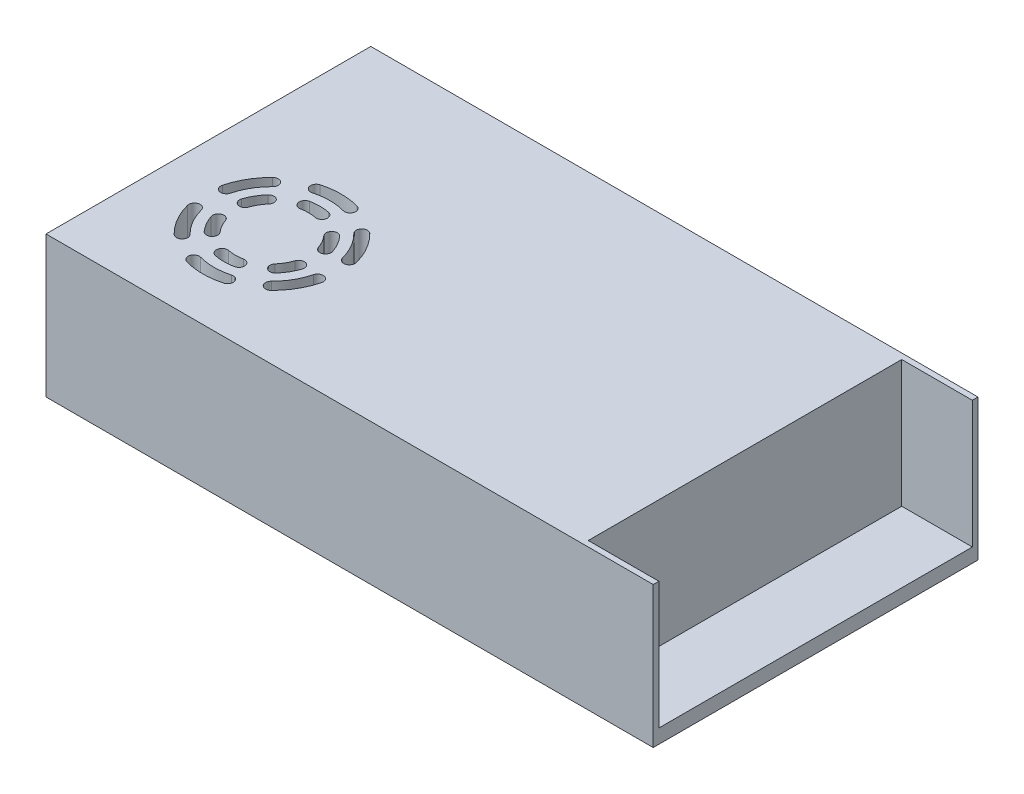
SolidWorks part; units mm, degrees
material "Простая углеродистая сталь"
ref_plane "Спереди" through (0, 0, 0) normal (0, 0, 1) x (1, 0, 0)
ref_plane "Сверху" through (0, 0, 0) normal (0, 1, 0) x (1, 0, 0)
ref_plane "Справа" through (0, 0, 0) normal (1, 0, 0) x (0, 0, -1)
sketch "Эскиз1" plane through (0, 0, 0) normal (0, 1, 0) x (1, 0, 0)
  line L0 (0, 0) -> (215, 0)
  line L1 (0, 0) -> (0, 115)
  line L2 (215, 0) -> (215, 115)
  line L3 (0, 115) -> (215, 115)
  dimension "D1" = 115
  dimension "D2" = 215
extrude "Бобышка-Вытянуть1" add sketch "Эскиз1" along normal blind 50
sketch "Эскиз2" plane through (0, 50, 0) normal (0, 1, 0) x (1, 0, 0)
  line L0 (215, 2) -> (190, 2)
  line L1 (215, 2) -> (215, 113)
  line L2 (190, 2) -> (190, 113)
  line L3 (215, 113) -> (190, 113)
  line L4 (215, 0) -> (215, 115) construction
  line L5 (215, 115) -> (0, 115) construction
  line L6 (0, 0) -> (215, 0) construction
  dimension "D1" = 2
  dimension "D2" = 2
  dimension "D3" = 25
extrude "Вырез-Вытянуть1" cut sketch "Эскиз2" against normal blind 45
sketch "Эскиз3" plane through (0, 50, 0) normal (0, 1, 0) x (1, 0, 0)
  line L0 (0, 115) -> (0, 0) construction
  line L1 (0, 0) -> (215, 0) construction
  line L2 (40, 17.5) -> (40, 62.5) construction
  circle A0 centre (40, 40) radius 22.5 construction
  arc A1 (37, 25.3031) -> (43, 25.3031) centre (40, 40) ccw construction
  arc A2 (36.6, 23.3435) -> (43.4, 23.3435) centre (40, 40) ccw
  circle A3 centre (40, 40) radius 15 construction
  arc A4 (37.4, 27.2627) -> (42.6, 27.2627) centre (40, 40) ccw
  arc A5 (37.4, 27.2627) -> (36.6, 23.3435) centre (37, 25.3031) ccw
  arc A6 (43.4, 23.3435) -> (42.6, 27.2627) centre (43, 25.3031) ccw
  arc A7 (25.7721, 35.2496) -> (28.7721, 30.0535) centre (40, 40) ccw construction
  arc A8 (23.875, 34.6162) -> (27.275, 28.7272) centre (40, 40) ccw
  arc A9 (27.6691, 35.883) -> (30.2691, 31.3797) centre (40, 40) ccw
  arc A10 (27.6691, 35.883) -> (23.875, 34.6162) centre (25.7721, 35.2496) ccw
  arc A11 (27.275, 28.7272) -> (30.2691, 31.3797) centre (28.7721, 30.0535) ccw
  arc A14 (28.7721, 49.9465) -> (25.7721, 44.7504) centre (40, 40) ccw construction
  arc A15 (27.275, 51.2728) -> (23.875, 45.3838) centre (40, 40) ccw
  arc A16 (30.2691, 48.6203) -> (27.6691, 44.117) centre (40, 40) ccw
  arc A17 (30.2691, 48.6203) -> (27.275, 51.2728) centre (28.7721, 49.9465) ccw
  arc A18 (23.875, 45.3838) -> (27.6691, 44.117) centre (25.7721, 44.7504) ccw
  arc A19 (43, 54.6969) -> (37, 54.6969) centre (40, 40) ccw construction
  arc A20 (43.4, 56.6565) -> (36.6, 56.6565) centre (40, 40) ccw
  arc A21 (42.6, 52.7373) -> (37.4, 52.7373) centre (40, 40) ccw
  arc A22 (42.6, 52.7373) -> (43.4, 56.6565) centre (43, 54.6969) ccw
  arc A23 (36.6, 56.6565) -> (37.4, 52.7373) centre (37, 54.6969) ccw
  arc A24 (54.2279, 44.7504) -> (51.2279, 49.9465) centre (40, 40) ccw construction
  arc A25 (56.125, 45.3838) -> (52.725, 51.2728) centre (40, 40) ccw
  arc A26 (52.3309, 44.117) -> (49.7309, 48.6203) centre (40, 40) ccw
  arc A27 (52.3309, 44.117) -> (56.125, 45.3838) centre (54.2279, 44.7504) ccw
  arc A28 (52.725, 51.2728) -> (49.7309, 48.6203) centre (51.2279, 49.9465) ccw
  arc A29 (51.2279, 30.0535) -> (54.2279, 35.2496) centre (40, 40) ccw construction
  arc A30 (52.725, 28.7272) -> (56.125, 34.6162) centre (40, 40) ccw
  arc A31 (49.7309, 31.3797) -> (52.3309, 35.883) centre (40, 40) ccw
  arc A32 (49.7309, 31.3797) -> (52.725, 28.7272) centre (51.2279, 30.0535) ccw
  arc A33 (56.125, 34.6162) -> (52.3309, 35.883) centre (54.2279, 35.2496) ccw
  arc A34 (34, 18.3148) -> (46, 18.3148) centre (40, 40) ccw construction
  arc A35 (33.4667, 16.3872) -> (46.5333, 16.3872) centre (40, 40) ccw
  arc A36 (34.5333, 20.2423) -> (45.4667, 20.2423) centre (40, 40) ccw
  arc A37 (34.5333, 20.2423) -> (33.4667, 16.3872) centre (34, 18.3148) ccw
  arc A38 (46.5333, 16.3872) -> (45.4667, 20.2423) centre (46, 18.3148) ccw
  arc A39 (18.22, 34.3535) -> (24.22, 23.9612) centre (40, 40) ccw construction
  arc A40 (16.284, 33.8516) -> (22.8174, 22.5356) centre (40, 40) ccw
  arc A41 (20.156, 34.8554) -> (25.6227, 25.3869) centre (40, 40) ccw
  arc A42 (20.156, 34.8554) -> (16.284, 33.8516) centre (18.22, 34.3535) ccw
  arc A43 (22.8174, 22.5356) -> (25.6227, 25.3869) centre (24.22, 23.9612) ccw
  arc A44 (24.22, 56.0388) -> (18.22, 45.6465) centre (40, 40) ccw construction
  arc A45 (22.8174, 57.4644) -> (16.284, 46.1484) centre (40, 40) ccw
  arc A46 (25.6227, 54.6131) -> (20.156, 45.1446) centre (40, 40) ccw
  arc A47 (25.6227, 54.6131) -> (22.8174, 57.4644) centre (24.22, 56.0388) ccw
  arc A48 (16.284, 46.1484) -> (20.156, 45.1446) centre (18.22, 45.6465) ccw
  arc A49 (46, 61.6852) -> (34, 61.6852) centre (40, 40) ccw construction
  arc A50 (46.5333, 63.6128) -> (33.4667, 63.6128) centre (40, 40) ccw
  arc A51 (45.4667, 59.7577) -> (34.5333, 59.7577) centre (40, 40) ccw
  arc A52 (45.4667, 59.7577) -> (46.5333, 63.6128) centre (46, 61.6852) ccw
  arc A53 (33.4667, 63.6128) -> (34.5333, 59.7577) centre (34, 61.6852) ccw
  arc A54 (61.78, 45.6465) -> (55.78, 56.0388) centre (40, 40) ccw construction
  arc A55 (63.716, 46.1484) -> (57.1826, 57.4644) centre (40, 40) ccw
  arc A56 (59.844, 45.1446) -> (54.3773, 54.6131) centre (40, 40) ccw
  arc A57 (59.844, 45.1446) -> (63.716, 46.1484) centre (61.78, 45.6465) ccw
  arc A58 (57.1826, 57.4644) -> (54.3773, 54.6131) centre (55.78, 56.0388) ccw
  arc A59 (55.78, 23.9612) -> (61.78, 34.3535) centre (40, 40) ccw construction
  arc A60 (57.1826, 22.5356) -> (63.716, 33.8516) centre (40, 40) ccw
  arc A61 (54.3773, 25.3869) -> (59.844, 34.8554) centre (40, 40) ccw
  arc A62 (54.3773, 25.3869) -> (57.1826, 22.5356) centre (55.78, 23.9612) ccw
  arc A63 (63.716, 33.8516) -> (59.844, 34.8554) centre (61.78, 34.3535) ccw
  point P10 (40, 25)
  point P16 (40, 40)
  point P17 (40, 40)
  point P23 (27.0096, 32.5)
  point P30 (27.0096, 47.5)
  point P37 (40, 55)
  point P44 (52.9904, 47.5)
  point P47 (40, 40)
  point P50 (25.7342, 35.3647)
  point P58 (52.9904, 32.5)
  point P63 (40, 40)
  point P65 (40, 17.5)
  point P74 (20.5144, 28.75)
  point P81 (20.5144, 51.25)
  point P88 (40, 62.5)
  point P95 (59.4856, 51.25)
  point P102 (59.4856, 28.75)
  point P107 (40, 40)
  dimension "D1" = 40
  dimension "D2" = 40
  dimension "D3" = 45
  dimension "D4" = 30
  dimension "D6" = 4
  dimension "D5" = 6
  dimension "D7" = 6
  dimension "D8" = 12
  dimension "D9" = 4
  dimension "D10" = 6
extrude "Вырез-Вытянуть3" cut sketch "Эскиз3" against normal blind 15
